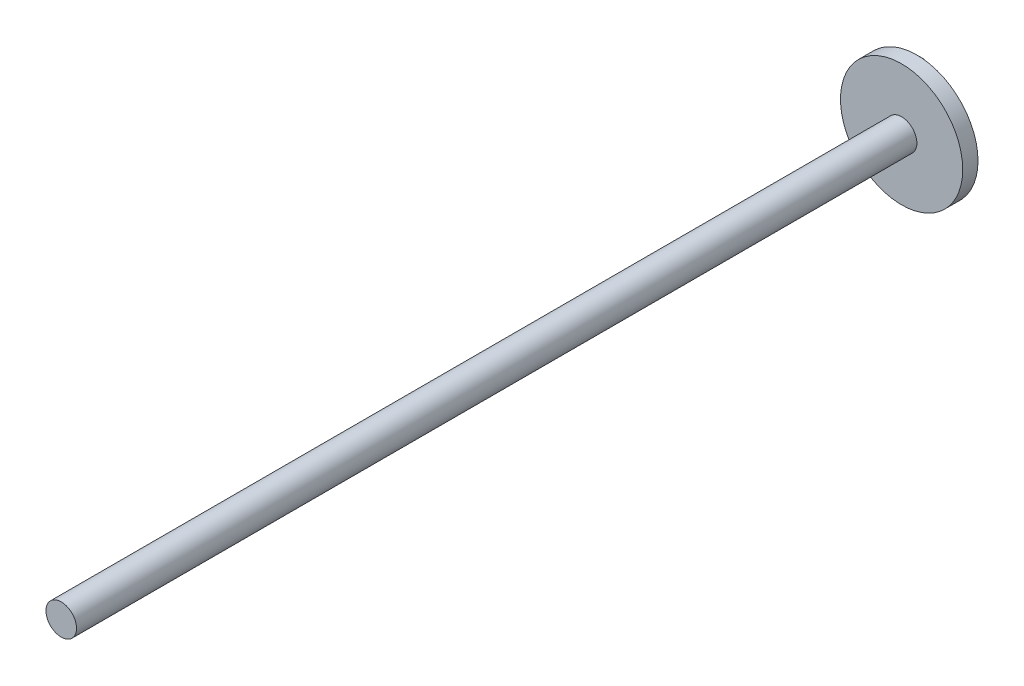
SolidWorks part; units mm, degrees
ref_plane "Front Plane" through (0, 0, 0) normal (0, 0, 1) x (1, 0, 0)
ref_plane "Top Plane" through (0, 0, 0) normal (0, 1, 0) x (1, 0, 0)
ref_plane "Right Plane" through (0, 0, 0) normal (1, 0, 0) x (0, 0, -1)
sketch "Sketch1" plane through (0, 0, 0) normal (0, 0, 1) x (1, 0, 0)
  circle A0 centre (0, 0) radius 40
  dimension "D1" = 80
extrude "Boss-Extrude1" add sketch "Sketch1" along normal blind 10
sketch "Sketch2" plane through (0, 0, 10) normal (0, 0, 1) x (1, 0, 0)
  circle A0 centre (0, 0) radius 10
extrude "Boss-Extrude2" add sketch "Sketch2" along normal blind 550
cosmetic thread "Cosmetic Thread1"
sketch "Sketch3" plane through (0, 0, 0) normal (0, 0, -1) x (-1, 0, 0)
  circle A0 centre (26.9986, 0) radius 10
extrude "Boss-Extrude3" add sketch "Sketch3" along normal blind 30
